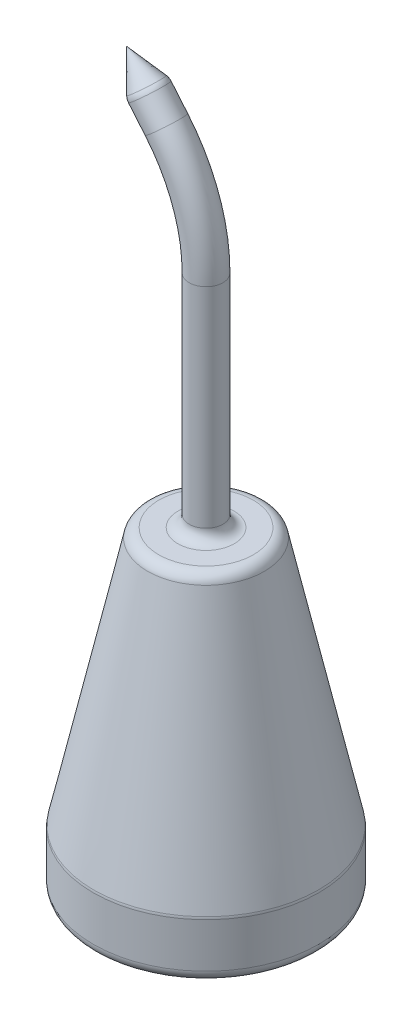
SolidWorks part; units mm, degrees
material "Chrome Stainless Steel"
ref_plane "Front Plane" through (0, 0, 0) normal (0, 0, 1) x (1, 0, 0)
ref_plane "Top Plane" through (0, 0, 0) normal (0, 1, 0) x (1, 0, 0)
ref_plane "Right Plane" through (0, 0, 0) normal (1, 0, 0) x (0, 0, -1)
sketch "Sketch1" plane through (0, 0, 0) normal (0, 0, 1) x (1, 0, 0)
  line L0 (10, 0) -> (20, 0)
  line L1 (20, 0) -> (20, 10.125)
  line L2 (20, 10.125) -> (10, 56)
  line L3 (10, 56) -> (0, 56)
  line L4 (0, 56) -> (0, 30)
  line L5 (0, 30) -> (10, 30)
  line L6 (10, 30) -> (10, 0)
  dimension "D1" = 10
  dimension "D2" = 20
  dimension "D3" = 56
  dimension "D4" = 30
  dimension "D5" = 10
ref_axis "Axis1" through (0, 42, 0) along (0, -1, 0)
revolve "Revolve1" add sketch "Sketch1" angle 360 about axis through (0, 42, 0) along (0, -1, 0)
sketch "Sketch2" plane through (0, 0, 0) normal (0, 0, 1) x (1, 0, 0)
  line L0 (0, 56) -> (0, 95.0809)
  line L1 (-7.0187, 114.3645) -> (-10.2846, 118.2567)
  line L2 (0, 0) -> (0, 56) construction
  line L3 (0, 56) -> (0, 106) construction
  line L4 (-10.2846, 118.2567) -> (0, 106) construction
  arc A0 (0, 95.0809) -> (-7.0187, 114.3645) centre (-30, 95.0809) ccw
  dimension "D3" = 30
  dimension "D1" = 50
  dimension "D2" = 140
  dimension "D4" = 56
  dimension "D6" = 16
ref_plane "Plane1" through (0, 0, 0) normal (0, 0, 1) x (1, 0, 0)
ref_plane "Plane2" through (0, 56, 0) normal (0, 1, 0) x (1, 0, 0)
sketch "Sketch4" plane through (0, 56, 0) normal (0, 1, 0) x (1, 0, 0)
  circle A0 centre (0, 0) radius 3
  dimension "D1" = 6
sweep "Sweep1" add profiles "Sketch4" path "Sketch2"
sketch "Sketch3" plane through (0, 0, 0) normal (0, 0, 1) x (1, 0, 0)
  line L0 (-10.2846, 118.2567) -> (-7.9865, 120.1851)
  line L1 (-7.9865, 120.1851) -> (-14.1413, 122.853)
  line L2 (-14.1413, 122.853) -> (-10.2846, 118.2567)
  line L3 (-4.7205, 116.2929) -> (-7.9865, 120.1851) construction
  point P0 (0, 0)
  dimension "D1" = 3
  dimension "D2" = 6
revolve "Revolve2" add sketch "Sketch3" angle 360 about L2
fillet "Fillet1" radius 2 5 edges at (0, 56, 10) (0, 0, 20) (-10.2846, 118.2567, 3) (0, 56, 3) (0, 10.125, 20)
